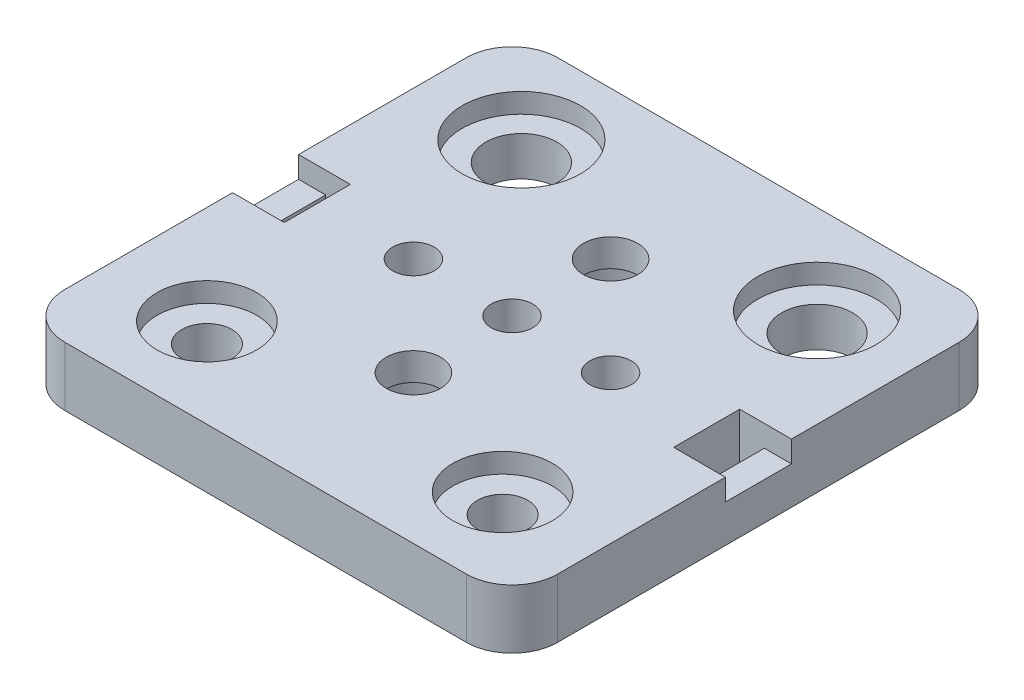
SolidWorks part; units mm, degrees
material "6061-T6 (SS)"
ref_plane "Front Plane" through (0, 0, 0) normal (0, 0, 1) x (1, 0, 0)
ref_plane "Top Plane" through (0, 0, 0) normal (0, 1, 0) x (1, 0, 0)
ref_plane "Right Plane" through (0, 0, 0) normal (1, 0, 0) x (0, 0, -1)
sketch "Sketch1" plane through (0, 0, 0) normal (0, 1, 0) x (1, 0, 0)
  line L0 (-23.7657, 0) -> (0, 0) construction
  line L1 (20.365, -25) -> (-20.365, -25)
  line L2 (25, -20.365) -> (25, 20.365)
  line L3 (20.365, 25) -> (-20.365, 25)
  line L4 (-25, -20.365) -> (-25, 20.365)
  line L5 (25, -25) -> (-25, 25) construction
  line L6 (25, 25) -> (-25, -25) construction
  line L7 (0, 0) -> (0, 28.9978) construction
  arc A0 (-20.365, 25) -> (-25, 20.365) centre (-20.365, 20.365) ccw
  arc A1 (25, 20.365) -> (20.365, 25) centre (20.365, 20.365) ccw
  arc A2 (-20.365, -25) -> (-25, -20.365) centre (-20.365, -20.365) cw
  arc A3 (20.365, -25) -> (25, -20.365) centre (20.365, -20.365) ccw
  circle A4 centre (-15, 15.95) radius 3.6
  circle A16 centre (15, 15.95) radius 3.6
  circle A33 centre (15, -15.95) radius 2.55
  circle A34 centre (-15, -15.95) radius 2.55
  point P0 (0, 0)
  dimension "D2" = 4.635
  dimension "D3" = 30
  dimension "D4" = 7.2
  dimension "D5" = 5.1
  dimension "D1" = 50
  dimension "D10" = 31.9
extrude "Boss-Extrude1" add sketch "Sketch1" along normal blind 6
hole_wizard "M5x0.8 Tapped Hole1" positions "Sketch4" profile "Sketch3" tap size "M5x0.8" standard "ANSI Metric" end condition through all
sketch "Sketch4" plane through (0, 6, 0) normal (0, 1, 0) x (1, 0, 0)
  line L0 (-17.7377, 0) -> (0, 0) construction
  line L1 (0, 0) -> (0, 30.1375) construction
  point P12 (0, 10)
  point P27 (-10, 0)
  point P31 (0, 0)
  point P34 (0, -10)
  point P36 (10, 0)
  dimension "D1" = 20
  dimension "D2" = 20
sketch "Sketch3" plane through (0, 6, -10) normal (1, 0, 0) x (0, 0, 1)
  line L0 (0, 0) -> (0, 6)
  line L1 (0, 6) -> (2.1, 6)
  line L2 (2.1, 6) -> (2.1, 0)
  line L5 (2.1, 0) -> (0, 0)
  line L11 (0, -6.35) -> (0, 107.95) construction
  dimension "Thread Major Dia." = 4.2
  dimension "Thru Tap Drill Depth" = 6
sketch "Sketch2" plane through (0, 6, 0) normal (0, 1, 0) x (1, 0, 0)
  circle A0 centre (-15, 15.95) radius 6
  circle A1 centre (15, 15.95) radius 6
  circle A2 centre (15, -15.95) radius 5.05
  circle A3 centre (-15, -15.95) radius 5.05
  dimension "D1" = 12
  dimension "D2" = 10.1
extrude "Cut-Extrude1" cut sketch "Sketch2" against normal blind 2
sketch "Sketch5" plane through (0, 6, 0) normal (0, 1, 0) x (1, 0, 0)
  line L0 (-25, 20.365) -> (-25, -20.365) construction
  line L1 (-25, 3.35) -> (-19.75, 3.35)
  line L2 (-25, 3.35) -> (-25, -3.35)
  line L3 (-25, -3.35) -> (-19.75, -3.35)
  line L4 (-19.75, 3.35) -> (-19.75, -3.35)
  line L5 (-19.75, 0) -> (0, 0) construction
  line L6 (0, 0) -> (0, 18.5468) construction
  line L7 (19.75, 3.35) -> (19.75, -3.35)
  line L8 (25, -3.35) -> (19.75, -3.35)
  line L9 (25, 3.35) -> (25, -3.35)
  line L10 (25, 3.35) -> (19.75, 3.35)
  dimension "D1" = 6.7
  dimension "D2" = 5.25
extrude "Cut-Extrude2" cut sketch "Sketch5" against normal blind 2.18
sketch "Sketch6" plane through (0, 3.82, 0) normal (0, 1, 0) x (1, 0, 0)
  line L0 (-25, -3.35) -> (-19.75, -3.35) construction
  line L1 (-19.75, 3.35) -> (-22.25, 3.35)
  line L2 (-19.75, 3.35) -> (-19.75, -3.35)
  line L3 (-19.75, -3.35) -> (-22.25, -3.35)
  line L4 (-22.25, 3.35) -> (-22.25, -3.35)
  line L5 (0, 0) -> (0, 14.6011) construction
  line L6 (22.25, 3.35) -> (22.25, -3.35)
  line L7 (19.75, -3.35) -> (22.25, -3.35)
  line L8 (19.75, 3.35) -> (19.75, -3.35)
  line L9 (19.75, 3.35) -> (22.25, 3.35)
  dimension "D1" = 2.5
extrude "Cut-Extrude3" cut sketch "Sketch6" against normal through all
hole_wizard "CBORE for M5 SHCS1" positions "Sketch8" profile "Sketch7" counterbore size "M5" standard "ANSI Metric" end condition through all
sketch "Sketch8" plane through (0, 0, 0) normal (0, -1, 0) x (-1, 0, 0)
  point P0 (0, 10)
  point P3 (0, -10)
sketch "Sketch7" plane through (0, 0, -10) normal (1, 0, 0) x (0, 0, -1)
  line L0 (0, 0) -> (0, 6)
  line L1 (0, 6) -> (2.75, 6)
  line L3 (2.75, 6) -> (2.75, 3.2)
  line L4 (2.75, 3.2) -> (5, 3.2)
  line L5 (5, 3.2) -> (5, 0)
  line L7 (5, 0) -> (0, 0)
  line L11 (0, -6.35) -> (0, 107.95) construction
  dimension "Thru Hole Dia." = 5.5
  dimension "Thru Hole Depth" = 6
  dimension "C'Bore Dia." = 10
  dimension "C'Bore Depth" = 3.2
